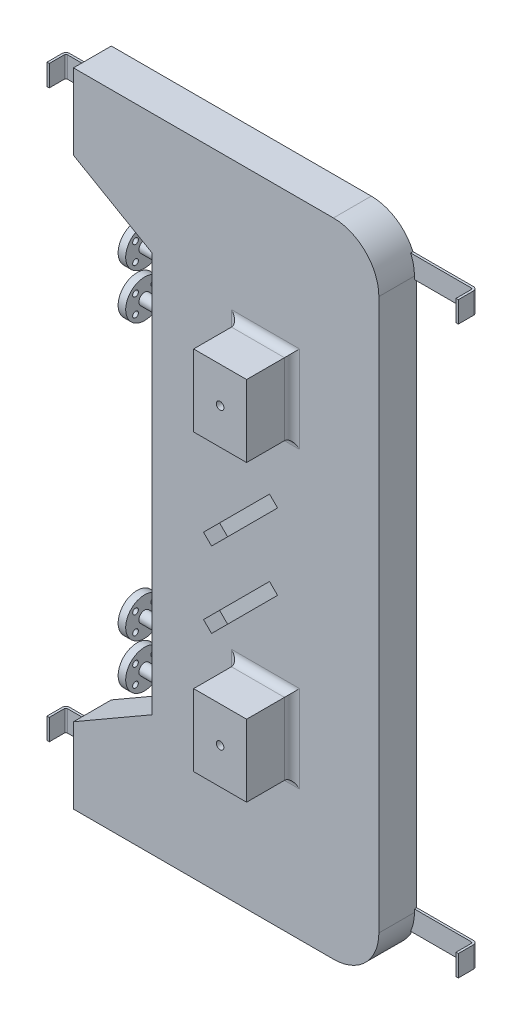
SolidWorks part; units mm, degrees
material "Cast Alloy Steel"
ref_plane "Front Plane" through (0, 0, 0) normal (0, 0, 1) x (1, 0, 0)
ref_plane "Top Plane" through (0, 0, 0) normal (0, 1, 0) x (1, 0, 0)
ref_plane "Right Plane" through (0, 0, 0) normal (1, 0, 0) x (0, 0, -1)
sketch "Sketch2" plane through (0, 0, 0) normal (0, 0, 1) x (1, 0, 0)
  line L4 (378.1273, 2218.2508) -> (169.8473, 2218.2508)
  line L5 (169.8473, 2218.2508) -> (169.8473, 2091.2508)
  line L6 (169.8473, 2091.2508) -> (301.9273, 2015.0508)
  line L7 (682.3269, 1679.6074) -> (-50.6643, 1679.6074) construction
  line L8 (378.1273, 1140.964) -> (606.1269, 1140.964)
  line L9 (682.3269, 1217.164) -> (682.3269, 2142.0508)
  line L10 (606.1269, 2218.2508) -> (378.1273, 2218.2508)
  line L11 (301.9273, 2142.0508) -> (301.9273, 1217.164)
  line L12 (378.1273, 1140.964) -> (606.1269, 1140.964)
  line L13 (682.3269, 1217.164) -> (682.3269, 2142.0508)
  line L14 (606.1269, 2218.2508) -> (378.1273, 2218.2508)
  line L15 (301.9273, 2142.0508) -> (301.9273, 1217.164)
  line L16 (378.1273, 1140.964) -> (169.8473, 1140.964)
  line L17 (169.8473, 1140.964) -> (169.8473, 1267.964)
  line L18 (169.8473, 1267.964) -> (301.9273, 1344.164)
  arc A8 (606.1269, 1140.964) -> (682.3269, 1217.164) centre (606.1269, 1217.164) ccw
  arc A9 (682.3269, 2142.0508) -> (606.1269, 2218.2508) centre (606.1269, 2142.0508) ccw
  arc A10 (378.1273, 2218.2508) -> (301.9273, 2142.0508) centre (378.1273, 2142.0508) ccw
  arc A11 (301.9273, 1217.164) -> (378.1273, 1140.964) centre (378.1273, 1217.164) ccw
  arc A12 (606.1269, 1140.964) -> (682.3269, 1217.164) centre (606.1269, 1217.164) ccw
  arc A13 (682.3269, 2142.0508) -> (606.1269, 2218.2508) centre (606.1269, 2142.0508) ccw
  arc A14 (378.1273, 2218.2508) -> (301.9273, 2142.0508) centre (378.1273, 2142.0508) ccw
  arc A15 (301.9273, 1217.164) -> (378.1273, 1140.964) centre (378.1273, 1217.164) ccw
  line M9 (378.1273, 1166.364) -> (606.1269, 1166.364)
  arc M10 (606.1269, 1166.364) -> (656.9269, 1217.164) centre (606.1269, 1217.164) ccw
  line M11 (656.9269, 1217.164) -> (656.9269, 2142.0508)
  arc M12 (656.9269, 2142.0508) -> (606.1269, 2192.8508) centre (606.1269, 2142.0508) ccw
  line M13 (606.1269, 2192.8508) -> (378.1273, 2192.8508)
  arc M14 (378.1273, 2192.8508) -> (327.3273, 2142.0508) centre (378.1273, 2142.0508) ccw
  line M15 (327.3273, 2142.0508) -> (327.3273, 1217.164)
  arc M16 (327.3273, 1217.164) -> (378.1273, 1166.364) centre (378.1273, 1217.164) ccw
  line M17 (384.4773, 1331.1638) -> (384.4773, 2028.051)
  arc M18 (384.4773, 2028.051) -> (599.7769, 2028.051) centre (492.1271, 2028.051) cw
  line M19 (599.7769, 2028.051) -> (599.7769, 1331.1638)
  arc M20 (599.7769, 1331.1638) -> (384.4773, 1331.1638) centre (492.1271, 1331.1638) cw
  dimension "D2" = 76.2
  dimension "D3" = 50.8
  dimension "D4" = 208.28
  dimension "D1" = 25.4
extrude "Boss-Extrude1" add sketch "Sketch2" along normal blind 63.5 contours A14 L4 L5 L6 L15 | L7 L13 A13 L14 A14 L15 M15 M14 M13 M12 M11 | L7 M11 M12 M13 M14 M15 M17 M18 M19 | L7 M19 M18 M17 | A15 L15 L18 L17 L16 | L13 L7 L15 A15 L12 A12 M11 M10 M9 M16 M15 | L7 M11 M19 M20 M17 M15 M16 M9 M10 | L7 M19 M17 M20
sketch "Sketch3" plane through (0, 0, 63.5) normal (0, 0, 1) x (1, 0, 0)
  line L0 (492.1271, 1420.364) -> (492.1271, 1445.2107) construction
  line L1 (492.1271, 1914.0041) -> (492.1271, 1938.8508) construction
  circle A0 centre (492.1271, 1350.514) radius 69.85 construction
  circle A1 centre (492.1271, 1515.0607) radius 69.85 construction
  circle A2 centre (492.1271, 1844.1541) radius 69.85 construction
  circle A3 centre (492.1271, 2008.7008) radius 69.85 construction
  circle A4 centre (492.1271, 1926.4275) radius 6.35
  circle A5 centre (492.1271, 1432.7873) radius 6.35
  dimension "D1" = 12.7
  dimension "D2" = 12.7
extrude "Cut-Extrude1" cut sketch "Sketch3" against normal up to next
sketch "Sketch5" plane through (0, 0, 63.5) normal (0, 0, 1) x (1, 0, 0)
  line L1 (447.6771, 1866.1025) -> (536.5771, 1866.1025)
  line L2 (447.6771, 1866.1025) -> (447.6771, 1986.7525)
  line L3 (447.6771, 1986.7525) -> (536.5771, 1986.7525)
  line L4 (536.5771, 1866.1025) -> (536.5771, 1986.7525)
  line L5 (447.6771, 1866.1025) -> (536.5771, 1986.7525) construction
  line L6 (447.6771, 1986.7525) -> (536.5771, 1866.1025) construction
  line L7 (447.6771, 1372.4623) -> (536.5771, 1372.4623)
  line L8 (447.6771, 1372.4623) -> (447.6771, 1493.1123)
  line L9 (447.6771, 1493.1123) -> (536.5771, 1493.1123)
  line L10 (536.5771, 1372.4623) -> (536.5771, 1493.1123)
  line L11 (447.6771, 1372.4623) -> (536.5771, 1493.1123) construction
  line L12 (447.6771, 1493.1123) -> (536.5771, 1372.4623) construction
  point P0 (492.1271, 1926.4275)
  point P6 (492.1271, 1432.7873)
  dimension "D1" = 120.65
  dimension "D2" = 88.9
extrude "Boss-Extrude2" add sketch "Sketch5" along normal blind 76.2
sketch "Sketch4" plane through (0, 0, 0) normal (0, 0, -1) x (-1, 0, 0)
  circle A0 centre (-492.1271, 1926.4275) radius 16.51
  circle A1 centre (-492.1271, 1926.4275) radius 6.35
  circle A2 centre (-492.1271, 1926.4275) radius 6.35 construction
  circle A3 centre (-492.1271, 1432.7873) radius 6.35
  circle A4 centre (-492.1271, 1432.7873) radius 6.35 construction
  circle A5 centre (-492.1271, 1432.7873) radius 16.51
  dimension "D1" = 0
  dimension "D2" = 0
  dimension "D3" = 10.16
  dimension "D4" = 10.16
extrude "Cut-Extrude2" cut sketch "Sketch4" against normal offset from surface (25.4 mm away) 38.1 up to face at (492.1271, 1926.4275, 63.5)
fillet "Fillet1" radius 12.7 8 edges at (447.6771, 1432.7873, 63.5) (492.1271, 1372.4623, 63.5) (536.5771, 1432.7873, 63.5) (492.1271, 1493.1123, 63.5) (447.6771, 1926.4275, 63.5) (492.1271, 1866.1025, 63.5) (492.1271, 1986.7525, 63.5) (536.5771, 1926.4275, 63.5)
sketch "Sketch6" plane through (0, 0, 139.7) normal (0, 0, 1) x (1, 0, 0)
  circle A1 centre (492.1271, 1926.4275) radius 6.35
  circle A2 centre (492.1271, 1926.4275) radius 6.35
  circle A3 centre (492.1271, 1432.7873) radius 6.35
  circle A4 centre (492.1271, 1432.7873) radius 6.35
  dimension "D1" = 0
  dimension "D2" = 0
extrude "Cut-Extrude3" cut sketch "Sketch6" against normal up to next
ref_plane "Plane1" through (387.9871, 0, 0) normal (-1, 0, 0) x (0, 0, 1)
ref_plane "Plane2" through (0, 1204.464, 0) normal (0, -1, 0) x (-1, 0, 0)
sketch "Sketch7" plane through (0, 1140.964, 0) normal (0, -1, 0) x (1, 0, 0)
  line L0 (93.6473, 31.75) -> (93.6473, 0)
  line L1 (93.6473, 0) -> (783.9269, 0)
  line L2 (783.9269, 0) -> (783.9269, 31.75)
  line L3 (169.8473, 0) -> (606.1269, 0) construction
  line L4 (169.8473, 63.5) -> (169.8473, 0) construction
  line L5 (682.3269, 63.5) -> (682.3269, 0) construction
  point P6 (169.8473, 31.75)
  dimension "D1" = 76.2
  dimension "D2" = 101.6
sketch "Sketch8" plane through (0, 1204.464, 0) normal (0, -1, 0) x (-1, 0, 0)
  line L3 (-93.6473, -31.75) -> (-93.6473, -6.35)
  line L4 (-99.9973, 0) -> (-777.5769, 0)
  line L5 (-783.9269, -6.35) -> (-783.9269, -31.75)
  line L6 (-169.8473, 0) -> (-606.1269, 0) construction
  line L7 (-169.8473, -63.5) -> (-169.8473, 0) construction
  line L8 (-682.3269, -63.5) -> (-682.3269, 0) construction
  line L9 (-169.8473, -63.5) -> (-169.8473, 0) construction
  arc A0 (-777.5769, 0) -> (-783.9269, -6.35) centre (-777.5769, -6.35) ccw
  arc A1 (-93.6473, -6.35) -> (-99.9973, 0) centre (-99.9973, -6.35) ccw
  point P10 (-169.8473, -31.75)
  dimension "D3" = 6.35
  dimension "D1" = 76.2
  dimension "D2" = 101.6
extrude "Extrude-Thin1" add sketch "Sketch8" along normal mid plane 35.56 thin thin type one direction reverse wall 3.81
ref_plane "Mid Plane" through (0, 1679.6074, 0) normal (0, -1, 0) x (-1, 0, 0)
mirror "Mirror1" about plane through (0, 1679.6074, 0) normal (0, -1, 0) of "Extrude-Thin1"
sketch "Sketch9" plane through (0, 0, 63.5) normal (0, 0, 1) x (1, 0, 0)
  line L0 (498.8623, 1763.313) -> (471.9215, 1736.3722)
  line L1 (498.8623, 1763.313) -> (512.3327, 1749.8426)
  line L2 (471.9215, 1736.3722) -> (485.3919, 1722.9018)
  line L3 (512.3327, 1749.8426) -> (485.3919, 1722.9018)
  line L4 (498.8623, 1763.313) -> (485.3919, 1722.9018) construction
  line L5 (471.9215, 1736.3722) -> (512.3327, 1749.8426) construction
  line L6 (682.3269, 1679.6074) -> (301.9273, 1679.6074) construction
  line L7 (682.3269, 1217.164) -> (682.3269, 2142.0508) construction
  line L8 (301.9273, 2015.0508) -> (301.9273, 1344.164) construction
  line L9 (498.8623, 1636.313) -> (471.9215, 1609.3722)
  line L10 (498.8623, 1636.313) -> (512.3327, 1622.8426)
  line L11 (471.9215, 1609.3722) -> (485.3919, 1595.9018)
  line L12 (512.3327, 1622.8426) -> (485.3919, 1595.9018)
  line L13 (498.8623, 1636.313) -> (485.3919, 1595.9018) construction
  line L14 (471.9215, 1609.3722) -> (512.3327, 1622.8426) construction
  line L15 (492.1271, 1743.1074) -> (492.1271, 1679.6074) construction
  line L16 (492.1271, 1679.6074) -> (492.1271, 1616.1074) construction
  point P1 (492.1271, 1743.1074)
  point P3 (492.1271, 1926.4275)
  point P14 (492.1271, 1616.1074)
  dimension "D1" = 45
  dimension "D2" = 19.05
  dimension "D3" = 38.1
  dimension "D4" = 63.5
  dimension "D5" = 45
extrude "Boss-Extrude3" add sketch "Sketch9" along normal offset from surface (83.82 mm away) 7.62 up to face at (498.4771, 1926.4275, 139.7) offset beyond the face yes
sketch "Sketch10" plane through (-555.2549, 555.2549, 0) normal (0.7071, -0.7071, 0) x (0, 0, -1)
  line L0 (-147.32, 1599.5995) -> (-147.32, 1561.4995) construction
  line L1 (-147.32, 1509.7969) -> (-147.32, 1471.6969) construction
  circle A0 centre (-128.27, 1490.7469) radius 9.525
  circle A1 centre (-128.27, 1580.5495) radius 9.525
  point P6 (-147.32, 1580.5495)
  point P7 (-147.32, 1490.7469)
  dimension "D1" = 19.05
  dimension "D2" = 19.05
extrude "Cut-Extrude4" cut sketch "Sketch10" against normal up to next
sketch "Sketch11" plane through (0, 1372.4623, 0) normal (0, -1, 0) x (1, 0, 0)
  line L0 (257.4773, 31.75) -> (365.4273, 31.75)
  line L1 (378.1273, 19.05) -> (378.1273, 0)
  line L3 (169.8473, 0) -> (606.1269, 0) construction
  line L4 (606.1269, 63.5) -> (606.1269, 0) construction
  arc A0 (365.4273, 31.75) -> (378.1273, 19.05) centre (365.4273, 19.05) cw
  point P4 (606.1269, 31.75)
  point P10 (378.1273, 31.75)
  dimension "D1" = 12.7
  dimension "D2" = 44.45
  dimension "D3" = 107.95
ref_plane "Plane4" through (257.4773, 0, 0) normal (-1, 0, 0) x (0, 0, 1)
sketch "Sketch12" plane through (257.4773, 0, 0) normal (-1, 0, 0) x (0, 0, 1)
  circle A0 centre (31.75, 1372.4623) radius 9.525
  dimension "D1" = 19.05
sweep "Sweep1" add profiles "Sketch12" path "Sketch11"
sketch "Sketch13" plane through (257.4773, 0, 0) normal (-1, 0, 0) x (0, 0, 1)
  line L0 (0, 2015.0508) -> (0, 1344.164) construction
  circle A0 centre (31.75, 1372.4623) radius 31.75
extrude "Boss-Extrude4" add sketch "Sketch13" along normal blind 12.7
sketch "Sketch14" plane through (0, 1372.4623, 0) normal (0, -1, 0) x (1, 0, 0)
  line L0 (257.4773, 31.75) -> (365.4273, 31.75) construction
  line L1 (378.1273, 19.05) -> (378.1273, 0) construction
  line L2 (257.4773, 31.75) -> (365.4273, 31.75)
  line L3 (378.1273, 19.05) -> (378.1273, 0)
  line L4 (257.4773, 31.75) -> (244.7773, 31.75)
  line L5 (244.7773, 63.5) -> (244.7773, 0) construction
  arc A0 (378.1273, 19.05) -> (365.4273, 31.75) centre (365.4273, 19.05) ccw construction
  arc A1 (378.1273, 19.05) -> (365.4273, 31.75) centre (365.4273, 19.05) ccw
sketch "Sketch15" plane through (244.7773, 0, 0) normal (-1, 0, 0) x (0, 0, 1)
  circle A2 centre (31.75, 1372.4623) radius 6.985
  circle A3 centre (31.75, 1372.4623) radius 6.985
  dimension "D1" = 2.54
sweep "Cut-Sweep1" cut profiles "Sketch15" path "Sketch14"
hole_wizard "3/8 (0.375) Diameter Hole1" positions "Sketch17" profile "Sketch16" hole size "3/8" standard "ANSI Inch"
sketch "Sketch17" plane through (244.7773, 0, 0) normal (-1, 0, 0) x (0, 0, 1)
  line L2 (31.75, 1372.4623) -> (57.5636, 1372.4623) construction
  line L3 (31.75, 1372.4623) -> (46.99, 1387.7023) construction
  circle A0 centre (31.75, 1372.4623) radius 31.75 construction
  circle A1 centre (31.75, 1372.4623) radius 6.985 construction
  point P0 (46.99, 1387.7023)
  point P19 (46.99, 1357.2223)
  point P20 (16.51, 1357.2223)
  point P21 (16.51, 1387.7023)
  dimension "D2" = 15.24
  dimension "D1" = 45
  dimension "D4" = 15.24
  dimension "D3" = 4
sketch "Sketch16" plane through (244.7773, 1387.7023, 46.99) normal (0, 1, 0) x (0, 0, 1)
  line L0 (0, 0) -> (0, 437.5496)
  line L1 (0, 437.5496) -> (4.7625, 437.5496)
  line L2 (4.7625, 437.5496) -> (4.7625, 0)
  line L5 (4.7625, 0) -> (0, 0)
  line L11 (0, -6.35) -> (0, 107.95) construction
  dimension "Thru Hole Dia." = 9.525
  dimension "Thru Hole Depth" = 437.5496
pattern_linear "LPattern1" count 2 spacing 76.2 along (0, 1, 0) of "Sweep1", "Boss-Extrude4", "Cut-Sweep1", "3/8 (0.375) Diameter Hole1"
mirror "Mirror2" about plane through (0, 1679.6074, 0) normal (0, -1, 0) of "LPattern1", "3/8 (0.375) Diameter Hole1", "Cut-Sweep1", "Boss-Extrude4", "Sweep1"
equation "\"D3@Sketch9\"=\"D2@Sketch9\"*2"
equation "\"D5@Sketch9\"=\"D1@Sketch9\""
equation "\"D4@Sketch17\"=\"D2@Sketch17\""
